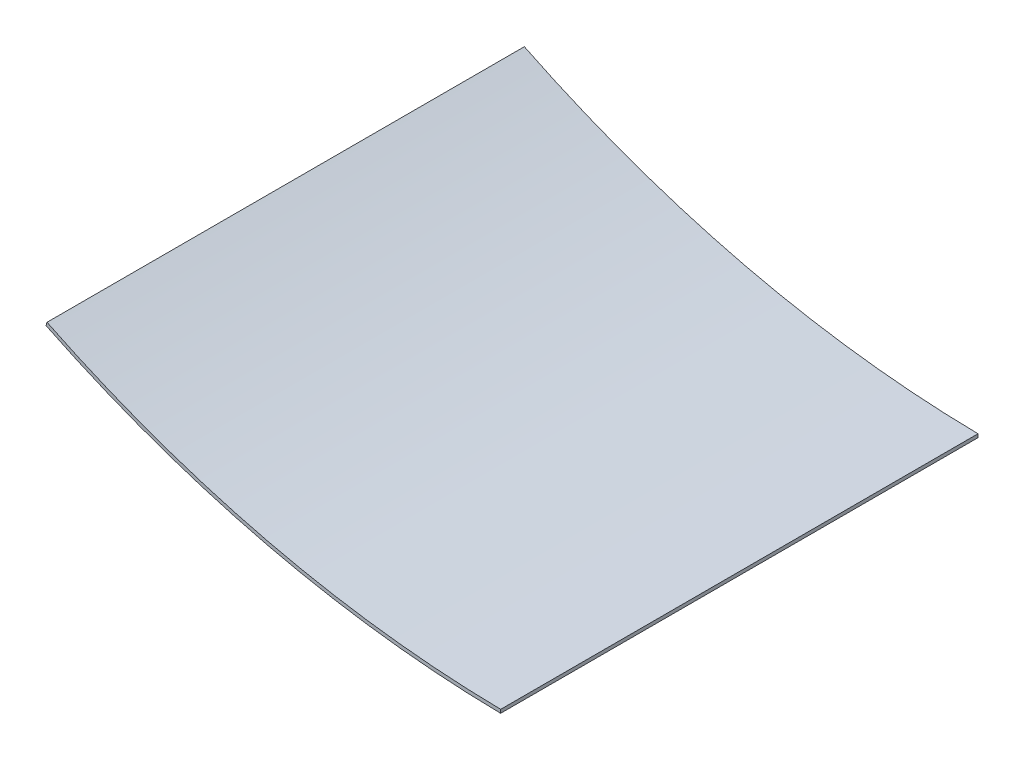
SolidWorks part; units mm, degrees
material "Acrylic (Medium-high impact)"
ref_plane "Front Plane" through (0, 0, 0) normal (0, 0, 1) x (1, 0, 0)
ref_plane "Top Plane" through (0, 0, 0) normal (0, 1, 0) x (1, 0, 0)
ref_plane "Right Plane" through (0, 0, 0) normal (1, 0, 0) x (0, 0, -1)
sketch "Sketch1" plane through (0, 0, 0) normal (0, 0, 1) x (1, 0, 0)
  line L2 (0, 242.9943) -> (-0.0449, 239.8196)
  line L3 (-413.0591, 341.6688) -> (-413.9908, 338.5903)
  arc A3 (0, 242.9943) -> (-413.0591, 341.6688) centre (13.752, 1214.4469) cw
  arc A4 (-0.0449, 239.8196) -> (-413.9908, 338.5903) centre (13.752, 1214.4469) cw
  arc A5 (-0.0449, 239.8196) -> (-414.4539, 338.8166) centre (13.752, 1214.4469) cw construction
  dimension "D1" = 3.175
extrude "Boss-Extrude1" add sketch "Sketch1" against normal up to surface (434.6 mm away)
